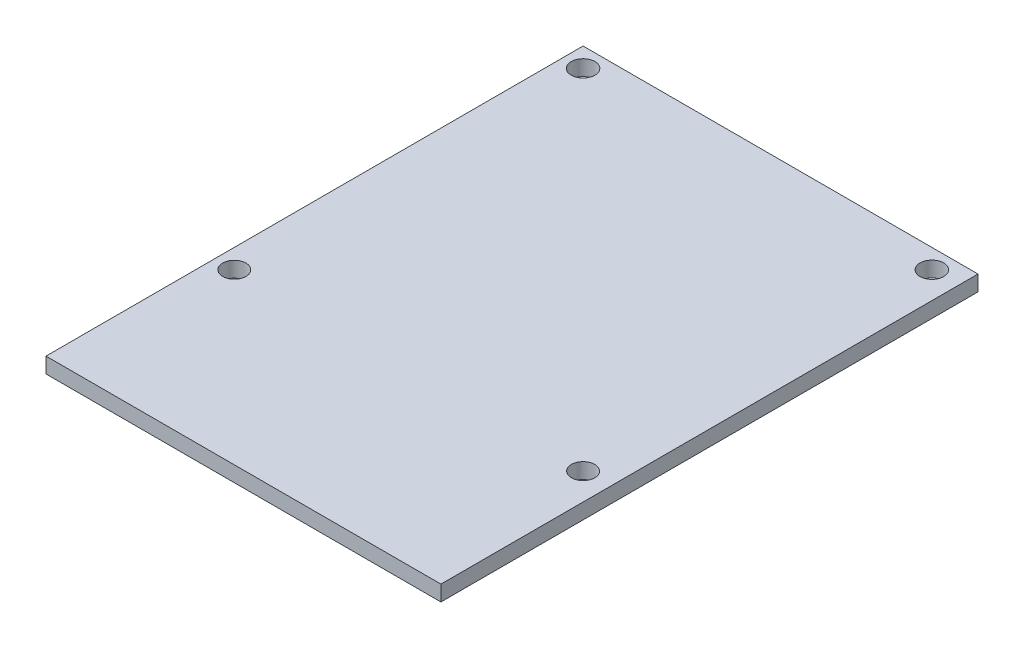
SolidWorks part; units mm, degrees
ref_plane "Front Plane" through (0, 0, 0) normal (0, 0, 1) x (1, 0, 0)
ref_plane "Top Plane" through (0, 0, 0) normal (0, 1, 0) x (1, 0, 0)
ref_plane "Right Plane" through (0, 0, 0) normal (1, 0, 0) x (0, 0, -1)
sketch "Sketch1" plane through (0, 0, 0) normal (0, 1, 0) x (1, 0, 0)
  line L1 (-25.4766, -34.6481) -> (25.4766, -34.6481)
  line L2 (-25.4766, -34.6481) -> (-25.4766, 34.6481)
  line L3 (-25.4766, 34.6481) -> (25.4766, 34.6481)
  line L4 (25.4766, -34.6481) -> (25.4766, 34.6481)
  line L5 (-25.4766, -34.6481) -> (25.4766, 34.6481) construction
  line L6 (-25.4766, 34.6481) -> (25.4766, -34.6481) construction
  circle A0 centre (-22.9766, 32.1481) radius 1.5286
  circle A1 centre (22.0234, 32.1481) radius 1.5286
  circle A2 centre (-22.9766, -12.8519) radius 1.5
  circle A3 centre (22.0234, -12.8519) radius 1.5
  point P0 (0, 0)
  point P14 (0, 0)
  point P15 (0, 0)
  dimension "D1" = 45
  dimension "D4" = 45
  dimension "D2" = 2.5
  dimension "D3" = 2.5
extrude "Boss-Extrude1" add sketch "Sketch1" along normal blind 2
